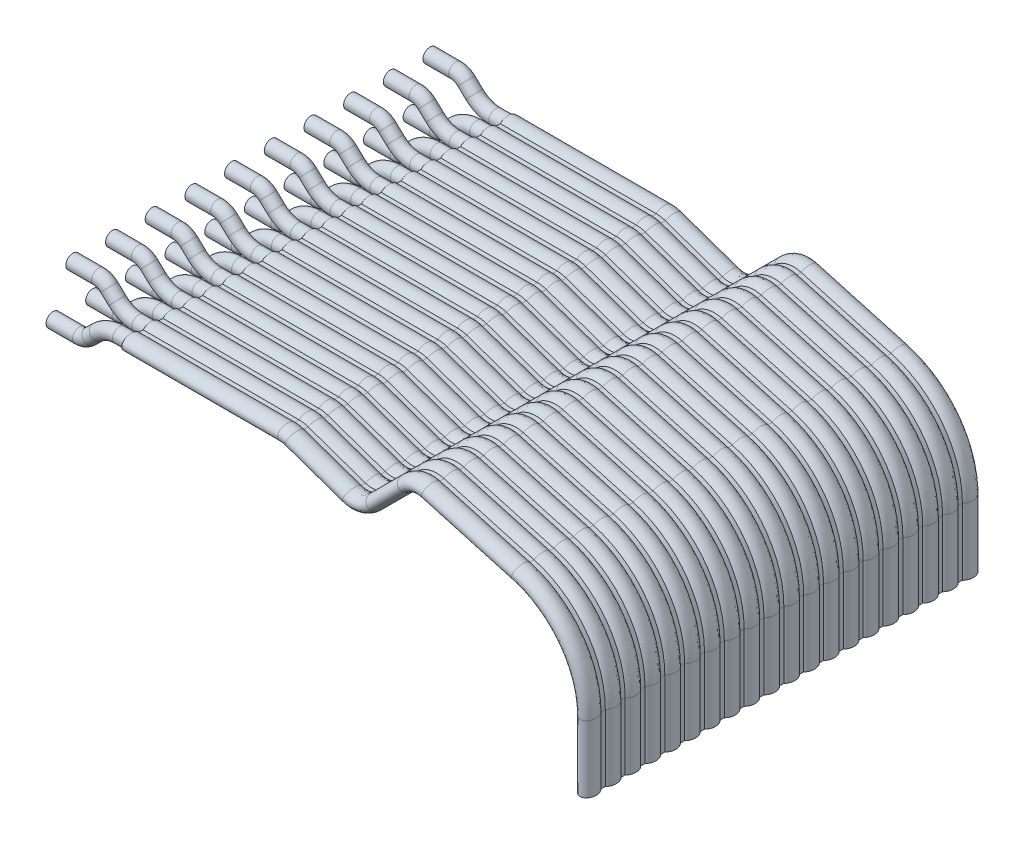
SolidWorks part; units mm, degrees
ref_plane "Front Plane" through (0, 0, 0) normal (0, 0, 1) x (1, 0, 0)
ref_plane "Top Plane" through (0, 0, 0) normal (0, 1, 0) x (1, 0, 0)
ref_plane "Right Plane" through (0, 0, 0) normal (1, 0, 0) x (0, 0, -1)
sketch "Sketch2" plane through (0, 0, 0) normal (0, 0, 1) x (1, 0, 0)
  line L0 (0, 0) -> (9.9828, 0)
  line L1 (29.3299, -6) -> (29.3299, -10.2749)
  line L2 (24.9524, -0.2235) -> (19.191, 1.3947)
  line L3 (17.7247, 1.0112) -> (15.7023, -1.0112)
  line L4 (14.1467, -1.3665) -> (10.4778, -0.084)
  arc A0 (24.9524, -0.2235) -> (29.3299, -6) centre (23.3299, -6) cw
  arc A1 (19.191, 1.3947) -> (17.7247, 1.0112) centre (18.7854, -0.0495) ccw
  arc A2 (15.7023, -1.0112) -> (14.1467, -1.3665) centre (14.6417, 0.0495) cw
  arc A3 (10.4778, -0.084) -> (9.9828, 0) centre (9.9828, -1.5) ccw
  point P5 (16.7135, 0)
  point P7 (29.3299, 0)
  dimension "D1" = 6
  dimension "D2" = 1.5
  dimension "D4" = 1.5
  dimension "D3" = 45
sketch "Sketch3" plane through (0, 0, 0) normal (1, 0, 0) x (0, 0, -1)
  line L0 (12.065, 0) -> (12.449, 0) construction
  line L1 (11.5661, 0.25) -> (11.2939, 0.25)
  line L3 (11.5661, -0.25) -> (11.2939, -0.25)
  line L5 (10.2961, 0.25) -> (10.0239, 0.25)
  line L6 (9.0261, 0.25) -> (8.7539, 0.25)
  line L7 (7.7561, 0.25) -> (7.4839, 0.25)
  line L8 (6.4861, 0.25) -> (6.2139, 0.25)
  line L9 (5.2161, 0.25) -> (4.9439, 0.25)
  line L10 (3.9461, 0.25) -> (3.6739, 0.25)
  line L11 (2.6761, 0.25) -> (2.4039, 0.25)
  line L12 (1.4061, 0.25) -> (1.1339, 0.25)
  line L13 (0.1361, 0.25) -> (-0.1361, 0.25)
  line L14 (-1.1339, 0.25) -> (-1.4061, 0.25)
  line L15 (-2.4039, 0.25) -> (-2.6761, 0.25)
  line L16 (-3.6739, 0.25) -> (-3.9461, 0.25)
  line L17 (-4.9439, 0.25) -> (-5.2161, 0.25)
  line L18 (-6.2139, 0.25) -> (-6.4861, 0.25)
  line L19 (-7.4839, 0.25) -> (-7.7561, 0.25)
  line L20 (-8.7539, 0.25) -> (-9.0261, 0.25)
  line L21 (-10.0239, 0.25) -> (-10.2961, 0.25)
  line L22 (-11.2939, 0.25) -> (-11.5661, 0.25)
  line L23 (-11.2939, -0.25) -> (-11.5661, -0.25)
  line L24 (-10.0239, -0.25) -> (-10.2961, -0.25)
  line L25 (-8.7539, -0.25) -> (-9.0261, -0.25)
  line L26 (-7.4839, -0.25) -> (-7.7561, -0.25)
  line L27 (-6.2139, -0.25) -> (-6.4861, -0.25)
  line L28 (-4.9439, -0.25) -> (-5.2161, -0.25)
  line L29 (-3.6739, -0.25) -> (-3.9461, -0.25)
  line L30 (-2.4039, -0.25) -> (-2.6761, -0.25)
  line L31 (-1.1339, -0.25) -> (-1.4061, -0.25)
  line L32 (0.1361, -0.25) -> (-0.1361, -0.25)
  line L33 (1.4061, -0.25) -> (1.1339, -0.25)
  line L34 (2.6761, -0.25) -> (2.4039, -0.25)
  line L35 (3.9461, -0.25) -> (3.6739, -0.25)
  line L36 (5.2161, -0.25) -> (4.9439, -0.25)
  line L37 (6.4861, -0.25) -> (6.2139, -0.25)
  line L38 (7.7561, -0.25) -> (7.4839, -0.25)
  line L39 (9.0261, -0.25) -> (8.7539, -0.25)
  line L40 (10.2961, -0.25) -> (10.0239, -0.25)
  line L41 (0, -0.25) -> (0, 0.25) construction
  ellipse E0 centre (12.065, 0) end of major axis (11.465, 0) minor radius 0.45 (11.5661, -0.25) -> (11.5661, 0.25) ccw
  ellipse E1 centre (10.795, 0) end of major axis (10.195, 0) minor radius 0.45 (11.2939, 0.25) -> (10.2961, 0.25) ccw
  ellipse E2 centre (9.525, 0) end of major axis (8.925, 0) minor radius 0.45 (10.0239, 0.25) -> (9.0261, 0.25) ccw
  ellipse E3 centre (8.255, 0) end of major axis (7.655, 0) minor radius 0.45 (8.7539, 0.25) -> (7.7561, 0.25) ccw
  ellipse E4 centre (6.985, 0) end of major axis (6.385, 0) minor radius 0.45 (7.4839, 0.25) -> (6.4861, 0.25) ccw
  ellipse E5 centre (5.715, 0) end of major axis (5.115, 0) minor radius 0.45 (6.2139, 0.25) -> (5.2161, 0.25) ccw
  ellipse E6 centre (4.445, 0) end of major axis (3.845, 0) minor radius 0.45 (4.9439, 0.25) -> (3.9461, 0.25) ccw
  ellipse E7 centre (3.175, 0) end of major axis (3.775, 0) minor radius 0.45 (3.6739, 0.25) -> (2.6761, 0.25) ccw
  ellipse E8 centre (1.905, 0) end of major axis (2.505, 0) minor radius 0.45 (2.4039, 0.25) -> (1.4061, 0.25) ccw
  ellipse E9 centre (0.635, 0) end of major axis (0.035, 0) minor radius 0.45 (1.1339, 0.25) -> (0.1361, 0.25) ccw
  ellipse E10 centre (-0.635, 0) end of major axis (-0.035, 0) minor radius 0.45 (-0.1361, 0.25) -> (-1.1339, 0.25) ccw
  ellipse E11 centre (-1.905, 0) end of major axis (-1.305, 0) minor radius 0.45 (-1.4061, 0.25) -> (-2.4039, 0.25) ccw
  ellipse E12 centre (-3.175, 0) end of major axis (-3.775, 0) minor radius 0.45 (-2.6761, 0.25) -> (-3.6739, 0.25) ccw
  ellipse E13 centre (-4.445, 0) end of major axis (-5.045, 0) minor radius 0.45 (-3.9461, 0.25) -> (-4.9439, 0.25) ccw
  ellipse E14 centre (-5.715, 0) end of major axis (-6.315, 0) minor radius 0.45 (-5.2161, 0.25) -> (-6.2139, 0.25) ccw
  ellipse E15 centre (-6.985, 0) end of major axis (-7.585, 0) minor radius 0.45 (-6.4861, 0.25) -> (-7.4839, 0.25) ccw
  ellipse E16 centre (-8.255, 0) end of major axis (-8.855, 0) minor radius 0.45 (-7.7561, 0.25) -> (-8.7539, 0.25) ccw
  ellipse E17 centre (-9.525, 0) end of major axis (-10.125, 0) minor radius 0.45 (-9.0261, 0.25) -> (-10.0239, 0.25) ccw
  ellipse E18 centre (-10.795, 0) end of major axis (-11.395, 0) minor radius 0.45 (-10.2961, 0.25) -> (-11.2939, 0.25) ccw
  ellipse E19 centre (-12.065, 0) end of major axis (-12.665, 0) minor radius 0.45 (-11.5661, 0.25) -> (-11.5661, -0.25) ccw
  ellipse E20 centre (10.795, 0) end of major axis (10.195, 0) minor radius 0.45 (10.2961, -0.25) -> (11.2939, -0.25) ccw
  ellipse E21 centre (9.525, 0) end of major axis (8.925, 0) minor radius 0.45 (9.0261, -0.25) -> (10.0239, -0.25) ccw
  ellipse E22 centre (8.255, 0) end of major axis (7.655, 0) minor radius 0.45 (7.7561, -0.25) -> (8.7539, -0.25) ccw
  ellipse E23 centre (6.985, 0) end of major axis (6.385, 0) minor radius 0.45 (6.4861, -0.25) -> (7.4839, -0.25) ccw
  ellipse E24 centre (5.715, 0) end of major axis (5.115, 0) minor radius 0.45 (5.2161, -0.25) -> (6.2139, -0.25) ccw
  ellipse E25 centre (4.445, 0) end of major axis (3.845, 0) minor radius 0.45 (3.9461, -0.25) -> (4.9439, -0.25) ccw
  ellipse E26 centre (3.175, 0) end of major axis (3.775, 0) minor radius 0.45 (2.6761, -0.25) -> (3.6739, -0.25) ccw
  ellipse E27 centre (1.905, 0) end of major axis (2.505, 0) minor radius 0.45 (1.4061, -0.25) -> (2.4039, -0.25) ccw
  ellipse E28 centre (0.635, 0) end of major axis (0.035, 0) minor radius 0.45 (0.1361, -0.25) -> (1.1339, -0.25) ccw
  ellipse E29 centre (-0.635, 0) end of major axis (-0.035, 0) minor radius 0.45 (-1.1339, -0.25) -> (-0.1361, -0.25) ccw
  ellipse E30 centre (-1.905, 0) end of major axis (-1.305, 0) minor radius 0.45 (-2.4039, -0.25) -> (-1.4061, -0.25) ccw
  ellipse E31 centre (-3.175, 0) end of major axis (-3.775, 0) minor radius 0.45 (-3.6739, -0.25) -> (-2.6761, -0.25) ccw
  ellipse E32 centre (-4.445, 0) end of major axis (-5.045, 0) minor radius 0.45 (-4.9439, -0.25) -> (-3.9461, -0.25) ccw
  ellipse E33 centre (-5.715, 0) end of major axis (-6.315, 0) minor radius 0.45 (-6.2139, -0.25) -> (-5.2161, -0.25) ccw
  ellipse E34 centre (-6.985, 0) end of major axis (-7.585, 0) minor radius 0.45 (-7.4839, -0.25) -> (-6.4861, -0.25) ccw
  ellipse E35 centre (-8.255, 0) end of major axis (-8.855, 0) minor radius 0.45 (-8.7539, -0.25) -> (-7.7561, -0.25) ccw
  ellipse E36 centre (-9.525, 0) end of major axis (-10.125, 0) minor radius 0.45 (-10.0239, -0.25) -> (-9.0261, -0.25) ccw
  ellipse E37 centre (-10.795, 0) end of major axis (-11.395, 0) minor radius 0.45 (-11.2939, -0.25) -> (-10.2961, -0.25) ccw
  dimension "D1" = 0.9
  dimension "D2" = 1.2
sweep "Main" add profiles "Sketch3" path "Sketch2"
sketch "Sketch5" plane through (0, 0, 0) normal (-1, 0, 0) x (0, 0, 1)
  circle A0 centre (0.635, 0) radius 0.45
  dimension "D1" = 0.9
  dimension "D2" = 0.635
sketch "Sketch6" plane through (0, 0, 0) normal (0, 0, 1) x (1, 0, 0)
  line L0 (0, 0) -> (-0.7833, 0)
  line L1 (-2.1569, 0.5463) -> (-2.6655, 1.0268)
  line L2 (-3.3523, 1.3) -> (-5, 1.3)
  arc A0 (-0.7833, 0) -> (-2.1569, 0.5463) centre (-0.7833, 2) cw
  arc A1 (-2.6655, 1.0268) -> (-3.3523, 1.3) centre (-3.3523, 0.3) ccw
  dimension "D1" = 1
  dimension "D4" = 2
  dimension "D2" = 5
  dimension "D3" = 1.3
sweep "pinUp" add profiles "Sketch5" path "Sketch6"
sketch "Sketch7" plane through (0, 0, 0) normal (0, 0, 1) x (1, 0, 0)
  line L0 (0, 0) -> (-0.7409, 0)
  line L1 (-2.1265, -0.5577) -> (-2.6089, -1.0211)
  line L2 (-3.3017, -1.3) -> (-5, -1.3)
  arc A0 (-2.6089, -1.0211) -> (-3.3017, -1.3) centre (-3.3017, -0.3) cw
  arc A1 (-0.7409, 0) -> (-2.1265, -0.5577) centre (-0.7409, -2) ccw
  point P10 (-2.1265, -0.5577)
  dimension "D1" = 1
  dimension "D3" = 2
  dimension "D2" = 1.3
sketch "Sketch8" plane through (0, 0, 0) normal (-1, 0, 0) x (0, 0, 1)
  circle A0 centre (-0.635, 0) radius 0.45
  point P2 (0, 0)
  dimension "D1" = 0.9
  dimension "D2" = 0.635
sweep "pinDown" add profiles "Sketch8" path "Sketch7"
pattern_linear "LPattern1" count 5 spacing 2.54 along (0, 0, -1) count 6 spacing 2.54 along (0, 0, 1) of "pinDown"
pattern_linear "LPattern2" count 5 spacing 2.54 along (0, 0, 1) count 6 spacing 2.54 along (0, 0, -1) of "pinUp"
